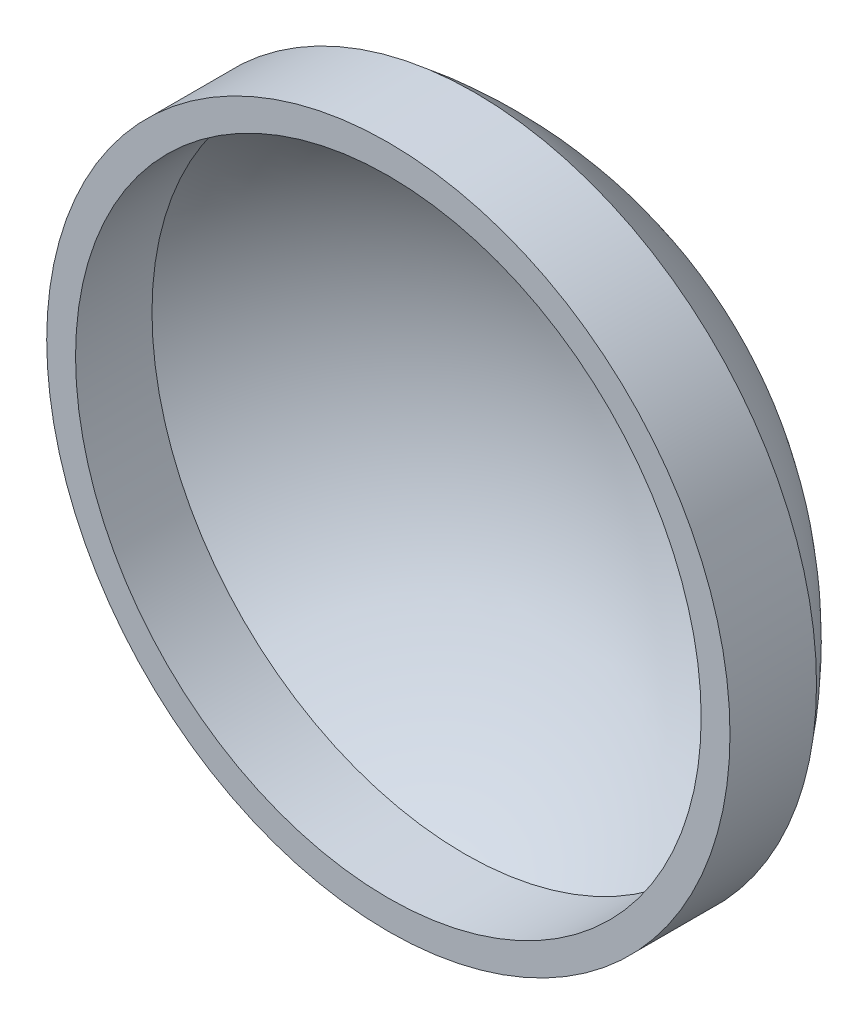
SolidWorks part; units mm, degrees
ref_plane "Front Plane" through (0, 0, 0) normal (0, 0, 1) x (1, 0, 0)
ref_plane "Top Plane" through (0, 0, 0) normal (0, 1, 0) x (1, 0, 0)
ref_plane "Right Plane" through (0, 0, 0) normal (1, 0, 0) x (0, 0, -1)
sketch "Sketch4" plane through (0, 0, 0) normal (0, 1, 0) x (1, 0, 0)
  line L0 (-125.4037, 0) -> (130.8958, 0) construction
  line L1 (0, 0) -> (0, 95.1207) construction
  line L2 (0, 38.1) -> (0, 15.748)
  line L3 (30.0923, 15.748) -> (30.0923, 23.368)
  line L4 (0, 15.748) -> (30.0923, 15.748)
  arc A1 (0, 38.1) -> (30.0923, 23.368) centre (0, 0) cw
  dimension "D1" = 38.1
  dimension "D2" = 15.748
  dimension "D3" = 7.62
  dimension "D4" = 22.352
  dimension "D5" = 30.0923
revolve "Revolve1" add sketch "Sketch4" angle 360 about L1
shell "Shell4" thickness 2.54
